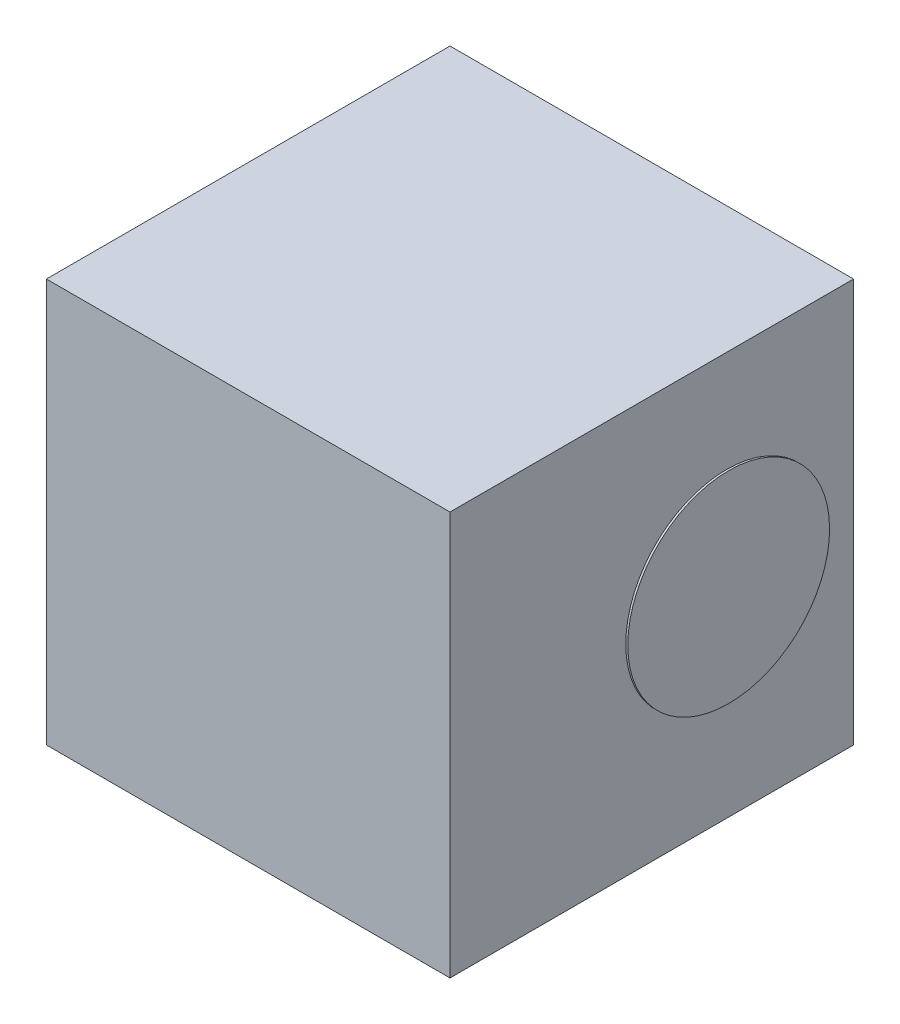
SolidWorks part; units mm, degrees
ref_plane "Front Plane" through (0, 0, 0) normal (0, 0, 1) x (1, 0, 0)
ref_plane "Top Plane" through (0, 0, 0) normal (0, 1, 0) x (1, 0, 0)
ref_plane "Right Plane" through (0, 0, 0) normal (1, 0, 0) x (0, 0, -1)
sketch "Sketch1" plane through (0, 0, 0) normal (0, 1, 0) x (1, 0, 0)
  line L0 (0, 0) -> (18.6879, 0) construction
  line L1 (0, 0) -> (0, -14.4281) construction
  line L3 (-1, 1) -> (1, 1)
  line L4 (-1, 1) -> (-1, -1)
  line L5 (-1, -1) -> (1, -1)
  line L6 (1, 1) -> (1, -1)
  dimension "D1" = 2
extrude "Boss-Extrude1" add sketch "Sketch1" along normal blind 2
sketch "Sketch2" plane through (1, 0, 0) normal (1, 0, 0) x (0, 0, -1)
  circle A1 centre (0.3711, 0.9971) radius 0.5
extrude "Boss-Extrude2" add sketch "Sketch2" along normal blind 0.01
